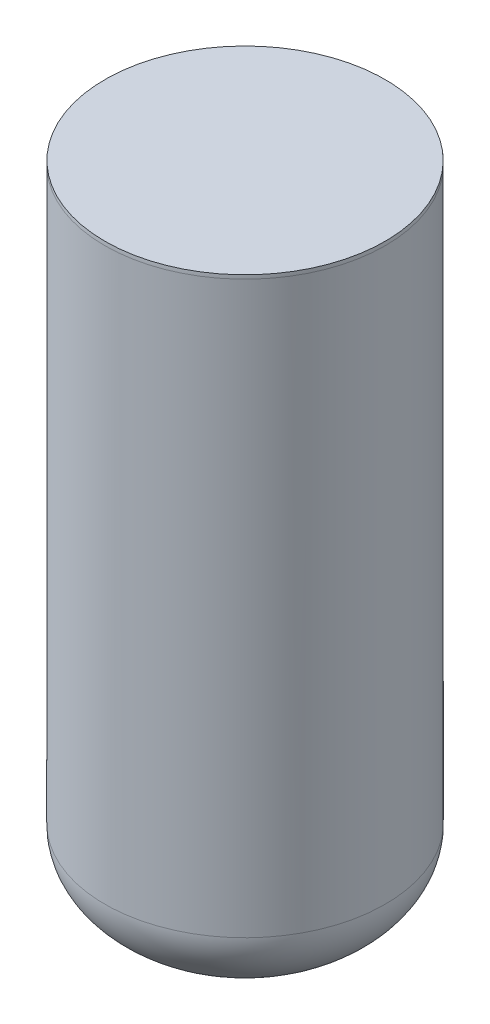
SolidWorks part; units mm, degrees
material "Kerosene"
ref_plane "Front Plane" through (0, 0, 0) normal (0, 0, 1) x (1, 0, 0)
ref_plane "Top Plane" through (0, 0, 0) normal (0, 1, 0) x (1, 0, 0)
ref_plane "Right Plane" through (0, 0, 0) normal (1, 0, 0) x (0, 0, -1)
sketch "Sketch2" plane through (0, 0, 0) normal (0, 1, 0) x (1, 0, 0)
  circle A0 centre (0, 0) radius 95.25
  dimension "D1" = 190.5
extrude "Boss-Extrude1" add sketch "Sketch2" along normal blind 387.35
sketch "Sketch3" plane through (0, 0, 0) normal (1, 0, 0) x (0, 0, -1)
  line L0 (95.25, 387.35) -> (-95.25, 387.35) construction
  line L1 (0, 447.04) -> (0, 387.35)
  line L2 (0, 387.35) -> (0, 447.04) construction
  line L3 (0, 387.35) -> (95.25, 387.35) construction
  line L4 (0, 387.35) -> (95.25, 387.35)
  ellipse E0 centre (0, 387.35) end of major axis (-95.25, 387.35) minor radius 59.69 (95.25, 387.35) -> (0, 447.04) ccw
  dimension "D1" = 59.69
revolve "Revolve2" add sketch "Sketch3" angle 360 about L1
sketch "Sketch4" plane through (0, 0, 0) normal (1, 0, 0) x (0, 0, -1)
  line L0 (0, -61.214) -> (0, 0)
  line L1 (0, 0) -> (95.25, 0)
  ellipse E0 centre (0, 0) end of major axis (95.25, 0) minor radius 61.214 (0, -61.214) -> (95.25, 0) ccw
  dimension "D1" = 61.214
revolve "Revolve3" add sketch "Sketch4" angle 360 about L0
ref_plane "Plane1" through (0, 447.04, 0) normal (0, 1, 0) x (1, 0, 0)
sketch "Sketch6" plane through (0, 447.04, 0) normal (0, 1, 0) x (1, 0, 0)
  circle A0 centre (0, 0) radius 95.25
extrude "7 Percent Ullage" cut sketch "Sketch6" against normal blind 57.15
